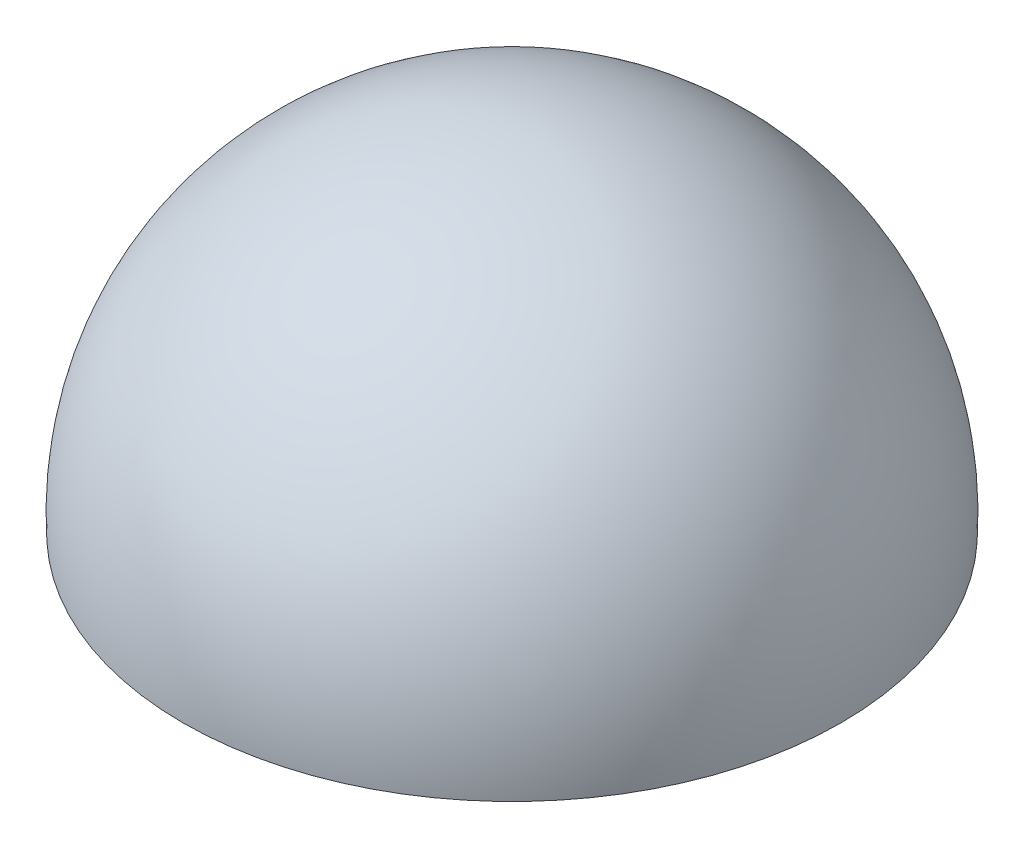
SolidWorks part; units mm, degrees
ref_plane "Plano frontal" through (0, 0, 0) normal (0, 0, 1) x (1, 0, 0)
ref_plane "Plano superior" through (0, 0, 0) normal (0, 1, 0) x (1, 0, 0)
ref_plane "Plano direito" through (0, 0, 0) normal (1, 0, 0) x (0, 0, -1)
sketch "Esboço1" plane through (0, 0, 0) normal (0, 0, 1) x (1, 0, 0)
  line L1 (0, -13.0718) -> (0, 15.9282)
  line L3 (-27.4963, -13.0718) -> (0, -13.0718)
  arc A0 (-27.4963, -13.0718) -> (0, 15.9282) centre (0, -11.607) cw
  point P4 (0, 0)
  point P11 (-13.7481, -13.0718)
revolve "Revolução2" add sketch "Esboço1" angle 360 about L1
sketch "Esboço2" plane through (0, 0, 0) normal (0, 0, 1) x (1, 0, 0)
  line L0 (0, -12.0718) -> (0, 14.9191)
  line L2 (-26.5, -12.0718) -> (0, -12.0718)
  line L3 (0, -12.0718) -> (0, 14.9282) construction
  arc A0 (-26.5, -12.0718) -> (0, 14.9191) centre (0, -11.5854) cw
  point P8 (0, -12.0718)
revolve "Corte-Revolução1" cut sketch "Esboço2" angle 360 about L0
